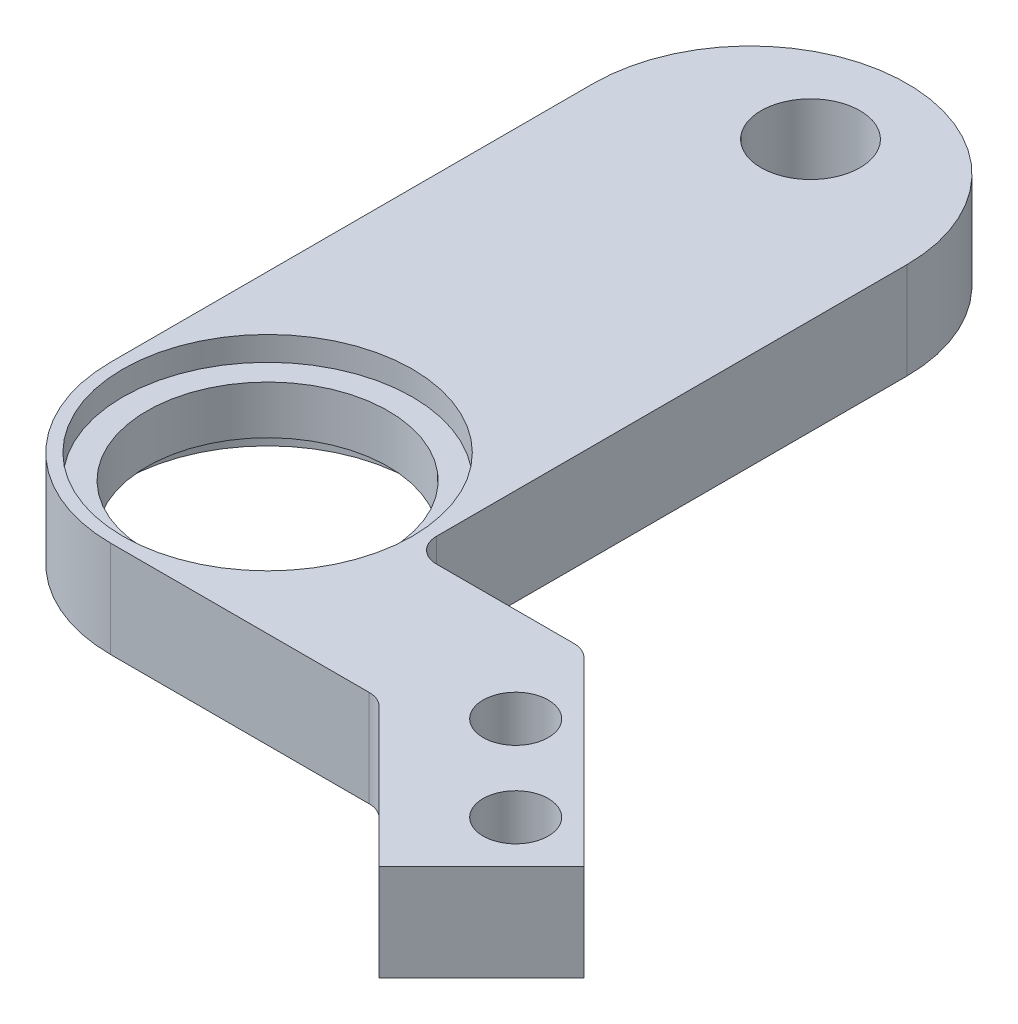
SolidWorks part; units mm, degrees
ref_plane "Front Plane" through (0, 0, 0) normal (0, 0, 1) x (1, 0, 0)
ref_plane "Top Plane" through (0, 0, 0) normal (0, 1, 0) x (1, 0, 0)
ref_plane "Right Plane" through (0, 0, 0) normal (1, 0, 0) x (0, 0, -1)
ref_plane "Plane1" through (0, -2, 0) normal (0, -1, 0) x (1, 0, 0)
sketch "Sketch1" plane through (0, -2, 0) normal (0, -1, 0) x (1, 0, 0)
  line L0 (11.1243, 26.5) -> (-6.5, 26.5)
  line L1 (-6.5, 26.5) -> (-6.5, 0)
  line L2 (6.5, 0) -> (6.5, 20.5)
  line L3 (6.5, 20.5) -> (13.6096, 20.5)
  line L4 (13.6096, 20.5) -> (13.6096, 36.1006)
  line L5 (13.6096, 36.1006) -> (11.1243, 38.5859)
  line L6 (11.1243, 38.5859) -> (11.1243, 26.5)
  arc A0 (-6.5, 0) -> (6.5, 0) centre (0, 0) ccw
extrude "Boss-Extrude1" add sketch "Sketch1" against normal blind 4
draft "Draft1" type of draft neutral plane draft angle 45 faces to draft 1 face at (13.6096, 0, 28.3003) neutral plane through (6.5, 2, 20.5) neutral plane normal (0, 0, -1) parameters "D1"=45
draft "Draft2" type of draft neutral plane draft angle 45 faces to draft 1 face at (11.1243, 0, 32.5429) neutral plane through (11.1243, 2, 26.5) neutral plane normal (0, 0, 1) parameters "D1"=45
ref_plane "Plane2" through (0, 0, 20) normal (0, 0, 1) x (1, 0, 0)
sketch "Sketch2" plane through (0, 0, 20) normal (0, 0, 1) x (1, 0, 0)
  line L0 (6, 2) -> (0, 2)
  line L1 (0, 2) -> (0, -2)
  line L2 (0, -2) -> (6, -2)
  line L3 (6, -2) -> (6, -1)
  line L4 (6, -1) -> (5, -1)
  line L5 (5, -1) -> (5, 1)
  line L6 (5, 1) -> (6, 1)
  line L7 (6, 1) -> (6, 2)
  line L8 (0, 2) -> (0, -2) construction
revolve "Cut-Revolve1" cut sketch "Sketch2" angle 360 about L8
hole_wizard "Ø4.1 (4.1) Diameter Hole1" positions "Sketch4" profile "Sketch3" hole size "Ø4.1" standard "ANSI Metric"
sketch "Sketch4" plane through (0, 2, 0) normal (0, 1, 0) x (1, 0, 0)
  point P0 (0, 2.5)
sketch "Sketch3" plane through (0, 2, -2.5) normal (1, 0, 0) x (0, 0, 1)
  line L0 (0, 0) -> (0, 4)
  line L1 (0, 4) -> (2.05, 4)
  line L2 (2.05, 4) -> (2.05, 0)
  line L5 (2.05, 0) -> (0, 0)
  line L11 (0, -6.35) -> (0, 107.95) construction
  dimension "Thru Hole Dia." = 4.1
  dimension "Thru Hole Depth" = 4
hole_wizard "Ø2.7 (2.7) Diameter Hole1" positions "Sketch6" profile "Sketch5" hole size "Ø2.7" standard "ANSI Metric"
sketch "Sketch6" plane through (0, -2, 0) normal (0, -1, 0) x (-1, 0, 0)
  point P0 (-14.6924, -24.4112)
  point P1 (-18.2279, -27.9467)
sketch "Sketch5" plane through (14.6924, -2, 24.4112) normal (1, 0, 0) x (0, 0, -1)
  line L0 (0, 0) -> (0, 4)
  line L1 (0, 4) -> (1.35, 4)
  line L2 (1.35, 4) -> (1.35, 0)
  line L5 (1.35, 0) -> (0, 0)
  line L11 (0, -6.35) -> (0, 107.95) construction
  dimension "Thru Hole Dia." = 2.7
  dimension "Thru Hole Depth" = 4
fillet "Fillet1" radius 1 3 edges at (6.5, 0, 20.5) (11.1243, 0, 26.5) (13.6096, 0, 20.5)
fillet "Fillet2" radius 6.5 1 edges at (-6.5, 0, 26.5)
